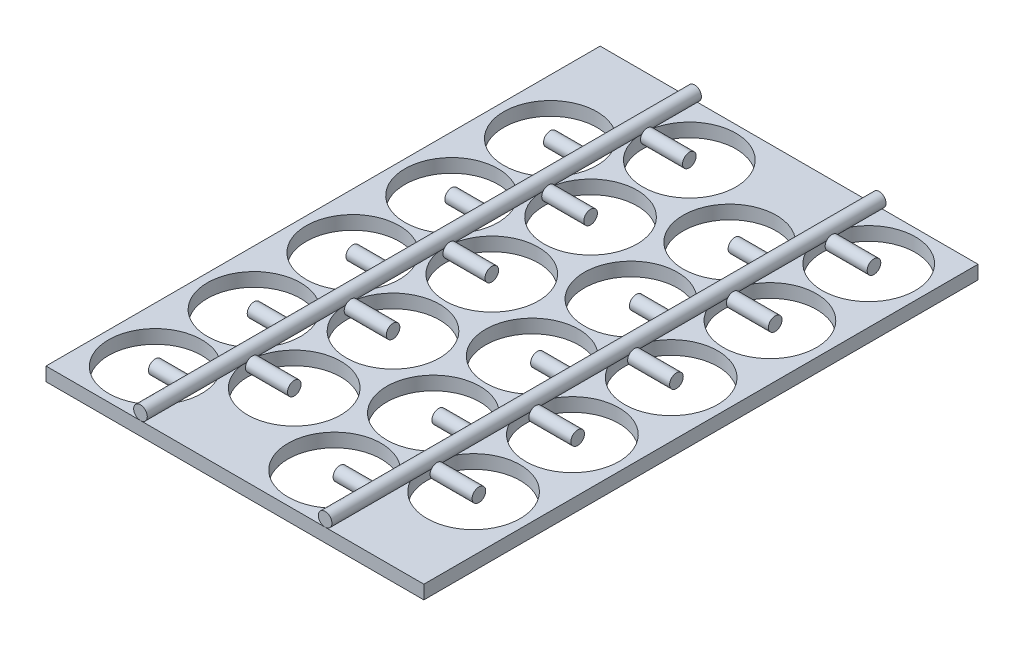
SolidWorks part; units mm, degrees
ref_plane "Front Plane" through (0, 0, 0) normal (0, 0, 1) x (1, 0, 0)
ref_plane "Top Plane" through (0, 0, 0) normal (0, 1, 0) x (1, 0, 0)
ref_plane "Right Plane" through (0, 0, 0) normal (1, 0, 0) x (0, 0, -1)
sketch "Sketch1" plane through (0, 0, 0) normal (0, 1, 0) x (1, 0, 0)
  line L0 (-9.15, 64.525) -> (-9.15, 32.2746) construction
  line L1 (-22, -64.525) -> (66, -64.525)
  line L2 (-22, -64.525) -> (-22, 64.525)
  line L3 (-22, 64.525) -> (66, 64.525)
  line L4 (22, -64.525) -> (22, 64.525) construction
  line L5 (-22, -64.525) -> (22, 64.525) construction
  line L6 (-22, 64.525) -> (22, -64.525) construction
  line L7 (-9.15, 40.075) -> (26.1125, 40.075) construction
  line L8 (-9.15, 40.075) -> (11.3748, 51.925) construction
  line L9 (66, -64.525) -> (66, 64.525)
  circle A2 centre (11.3748, 51.925) radius 10.85
  circle A3 centre (-9.15, 40.075) radius 10.85
  circle A4 centre (-9.1548, 17.075) radius 10.85
  circle A5 centre (11.37, 28.925) radius 10.85
  circle A6 centre (-9.1596, -5.925) radius 10.85
  circle A7 centre (11.3652, 5.925) radius 10.85
  circle A8 centre (-9.1644, -28.925) radius 10.85
  circle A9 centre (11.3604, -17.075) radius 10.85
  circle A10 centre (-9.1692, -51.925) radius 10.85
  circle A11 centre (11.3556, -40.075) radius 10.85
  circle A12 centre (53.15, 51.925) radius 10.85
  circle A13 centre (32.6252, 40.075) radius 10.85
  circle A14 centre (53.1452, 28.925) radius 10.85
  circle A15 centre (32.6204, 17.075) radius 10.85
  circle A16 centre (53.1404, 5.925) radius 10.85
  circle A17 centre (32.6156, -5.925) radius 10.85
  circle A18 centre (53.1356, -17.075) radius 10.85
  circle A19 centre (32.6108, -28.925) radius 10.85
  circle A20 centre (53.1308, -40.075) radius 10.85
  circle A21 centre (32.606, -51.925) radius 10.85
  point P0 (0, 0)
  dimension "D3" = 21.7
  dimension "D4" = 21.7
  dimension "D5" = 2
  dimension "D6" = 60
  dimension "D7" = 5
  dimension "D8" = 1.75
  dimension "D9" = 2
  dimension "D10" = 2
  dimension "D2" = 1.75
  dimension "D11" = 2
  dimension "D1" = 44
extrude "Boss-Extrude2" add sketch "Sketch1" along normal blind 3.175 contours L3 L4 L1 L2
sketch "Sketch2" plane through (0, 0, 64.525) normal (0, 0, 1) x (1, 0, 0)
  line L0 (-22, 3.175) -> (66, 3.175) construction
  circle A0 centre (0, 4.7625) radius 1.5875
  dimension "D1" = 3.175
extrude "Boss-Extrude3" add sketch "Sketch2" against normal up to surface (129.05 mm away) separate body up to face at (22, 1.5875, -64.525)
sketch "Sketch4" plane through (0, 3.175, 0) normal (0, 1, 0) x (1, 0, 0)
  line L0 (11.3748, 51.925) -> (1.5875, 51.925)
  line L1 (1.5875, -64.525) -> (1.5875, 64.525) construction
  line L13 (11.3748, 51.925) -> (1.5875, 51.925)
  line L14 (11.3748, 51.925) -> (11.3748, 53.5125)
  line L15 (11.3748, 53.5125) -> (1.5875, 53.5125)
  line L16 (1.5875, 51.925) -> (1.5875, 53.5125)
  dimension "D1" = 1.5875
ref_plane "Plane1" through (22, 0, 0) normal (1, 0, 0) x (0, 0, -1)
revolve "Revolve3" add sketch "Sketch4" angle 360 about L0
sketch "Sketch7" plane through (0, 3.175, 0) normal (0, 1, 0) x (1, 0, 0)
  line L0 (-9.15, 40.075) -> (-1.5875, 40.075)
  line L1 (-1.5875, 64.525) -> (-1.5875, -64.525) construction
  line L2 (-1.5875, 40.075) -> (-1.5875, 41.6625)
  line L3 (-1.5875, 41.6625) -> (-9.15, 41.6625)
  line L4 (-9.15, 41.6625) -> (-9.15, 40.075)
  dimension "D1" = 1.5875
revolve "Revolve4" add sketch "Sketch7" angle 360 about L0
pattern_linear "LPattern2" count 5 spacing 23 along (0, 0, 1) of bodies 116
pattern_linear "LPattern3" count 5 spacing 23 along (0, 0, 1) of bodies 115
pattern_linear "LPattern4" count 2 spacing 43 along (1, 0, 0) of bodies 120 124 119 123 118 122 117 121 102 115 116
